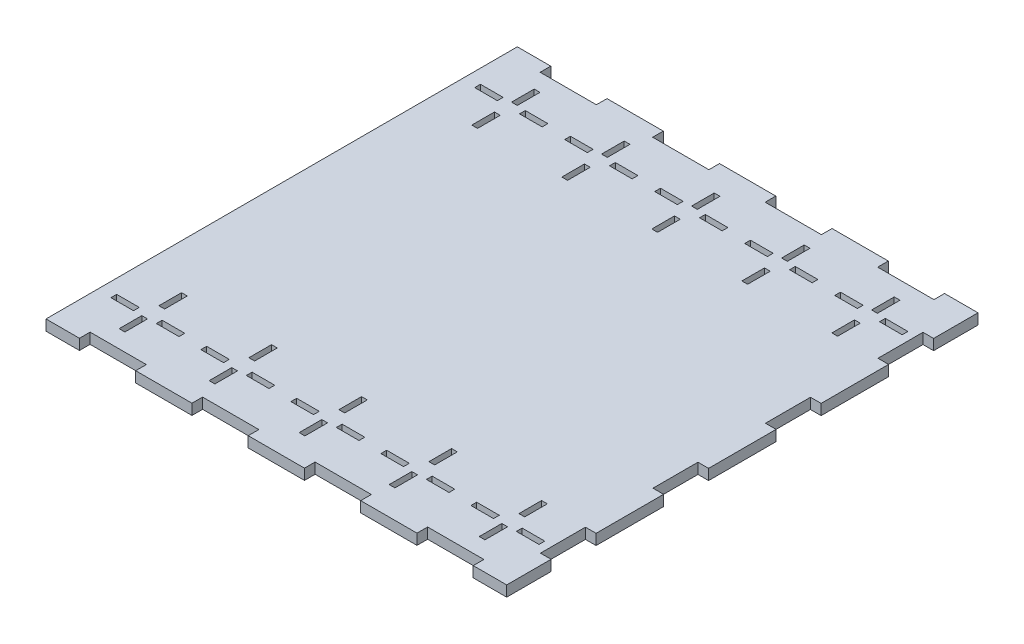
SolidWorks part; units mm, degrees
material "Balsa"
ref_plane "Front Plane" through (0, 0, 0) normal (0, 0, 1) x (1, 0, 0)
ref_plane "Top Plane" through (0, 0, 0) normal (0, 1, 0) x (1, 0, 0)
ref_plane "Right Plane" through (0, 0, 0) normal (1, 0, 0) x (0, 0, -1)
sketch "Sketch1" plane through (0, 0, 0) normal (0, 1, 0) x (1, 0, 0)
  line L0 (0, 133) -> (0, -133) construction
  line L1 (-130, -133) -> (130, -133)
  line L2 (-130, -133) -> (-130, 133)
  line L3 (-130, 133) -> (130, 133)
  line L4 (130, -133) -> (130, 133)
  point P4 (0, 133)
  point P6 (130, 0)
  dimension "D1" = 266
  dimension "D2" = 260
extrude "Boss-Extrude1" add sketch "Sketch1" along normal blind 6 contours L3 L4 L1 L2
sketch "Sketch2" plane through (0, 6, 0) normal (0, 1, 0) x (1, 0, 0)
  line L0 (-130, 0) -> (130, 0) construction
  line L1 (-130, -133) -> (-130, 133) construction
  line L2 (130, -133) -> (130, 133) construction
  line L3 (0, 133) -> (0, -133) construction
  line L4 (-130, 133) -> (130, 133) construction
  line L5 (-130, -133) -> (130, -133) construction
  line L6 (111.125, 133) -> (111.125, 127)
  line L7 (-15.875, 133) -> (-47.625, 133)
  line L8 (-15.875, 133) -> (-15.875, 127)
  line L9 (-15.875, 127) -> (-47.625, 127)
  line L10 (-47.625, 133) -> (-47.625, 127)
  line L11 (-79.375, 133) -> (-111.125, 133)
  line L12 (-79.375, 133) -> (-79.375, 127)
  line L13 (-79.375, 127) -> (-111.125, 127)
  line L14 (-111.125, 133) -> (-111.125, 127)
  line L15 (79.375, 127) -> (111.125, 127)
  line L16 (79.375, 133) -> (79.375, 127)
  line L17 (79.375, 133) -> (111.125, 133)
  line L18 (47.625, 133) -> (47.625, 127)
  line L19 (15.875, 127) -> (47.625, 127)
  line L20 (15.875, 133) -> (15.875, 127)
  line L21 (15.875, 133) -> (47.625, 133)
  line L22 (15.875, -133) -> (47.625, -133)
  line L23 (15.875, -133) -> (15.875, -127)
  line L24 (15.875, -127) -> (47.625, -127)
  line L25 (47.625, -133) -> (47.625, -127)
  line L26 (79.375, -133) -> (111.125, -133)
  line L27 (79.375, -133) -> (79.375, -127)
  line L28 (79.375, -127) -> (111.125, -127)
  line L29 (-111.125, -133) -> (-111.125, -127)
  line L30 (-79.375, -127) -> (-111.125, -127)
  line L31 (-79.375, -133) -> (-79.375, -127)
  line L32 (-79.375, -133) -> (-111.125, -133)
  line L33 (-47.625, -133) -> (-47.625, -127)
  line L34 (-15.875, -127) -> (-47.625, -127)
  line L35 (-15.875, -133) -> (-15.875, -127)
  line L36 (-15.875, -133) -> (-47.625, -133)
  line L37 (111.125, -133) -> (111.125, -127)
  line L38 (130, 133) -> (0, 0) construction
  line L39 (124, -82.55) -> (124, -107.95)
  line L40 (130, 19.05) -> (124, 19.05)
  line L41 (130, 19.05) -> (130, 44.45)
  line L42 (130, 44.45) -> (124, 44.45)
  line L43 (124, 19.05) -> (124, 44.45)
  line L44 (130, 82.55) -> (124, 82.55)
  line L45 (130, 82.55) -> (130, 107.95)
  line L46 (130, 107.95) -> (124, 107.95)
  line L47 (124, 82.55) -> (124, 107.95)
  line L48 (130, -107.95) -> (124, -107.95)
  line L49 (130, -82.55) -> (130, -107.95)
  line L50 (130, -82.55) -> (124, -82.55)
  line L51 (124, -19.05) -> (124, -44.45)
  line L52 (130, -44.45) -> (124, -44.45)
  line L53 (130, -19.05) -> (130, -44.45)
  line L54 (130, -19.05) -> (124, -19.05)
  point P12 (0, 0)
  point P22 (-31.75, 127)
  point P23 (-95.25, 127)
  point P59 (124, 31.75)
  point P60 (130, 31.75)
  point P61 (130, 95.25)
  dimension "D1" = 31.75
  dimension "D2" = 63.5
  dimension "D3" = 63.5
  dimension "D4" = 254
  dimension "D5" = 63.5
  dimension "D6" = 25.4
  dimension "D7" = 63.5
extrude "Tab Cut Outs" cut sketch "Sketch2" against normal up to surface (6 mm away) up to face at (0, 0, 0)
sketch "Sketch3" plane through (0, 6, 0) normal (0, 1, 0) x (1, 0, 0)
  line L104 (79.4766, -127.1016) -> (111.0234, -127.1016)
  line L105 (111.0234, -127.1016) -> (111.0234, -133.1016)
  line L106 (111.0234, -133.1016) -> (130.1016, -133.1016)
  line L107 (130.1016, -133.1016) -> (130.1016, -107.8484)
  line L108 (130.1016, -107.8484) -> (124.1016, -107.8484)
  line L109 (124.1016, -107.8484) -> (124.1016, -82.6516)
  line L110 (124.1016, -82.6516) -> (130.1016, -82.6516)
  line L111 (130.1016, -82.6516) -> (130.1016, -44.3484)
  line L112 (130.1016, -44.3484) -> (124.1016, -44.3484)
  line L113 (124.1016, -44.3484) -> (124.1016, -19.1516)
  line L114 (124.1016, -19.1516) -> (130.1016, -19.1516)
  line L115 (130.1016, -19.1516) -> (130.1016, 19.1516)
  line L116 (130.1016, 19.1516) -> (124.1016, 19.1516)
  line L117 (124.1016, 19.1516) -> (124.1016, 44.3484)
  line L118 (124.1016, 44.3484) -> (130.1016, 44.3484)
  line L119 (130.1016, 44.3484) -> (130.1016, 82.6516)
  line L120 (130.1016, 82.6516) -> (124.1016, 82.6516)
  line L121 (124.1016, 82.6516) -> (124.1016, 107.8484)
  line L122 (124.1016, 107.8484) -> (130.1016, 107.8484)
  line L123 (130.1016, 107.8484) -> (130.1016, 133.1016)
  line L124 (130.1016, 133.1016) -> (111.0234, 133.1016)
  line L125 (111.0234, 133.1016) -> (111.0234, 127.1016)
  line L126 (111.0234, 127.1016) -> (79.4766, 127.1016)
  line L127 (79.4766, 127.1016) -> (79.4766, 133.1016)
  line L128 (79.4766, 133.1016) -> (47.5234, 133.1016)
  line L129 (47.5234, 133.1016) -> (47.5234, 127.1016)
  line L130 (47.5234, 127.1016) -> (15.9766, 127.1016)
  line L131 (15.9766, 127.1016) -> (15.9766, 133.1016)
  line L132 (15.9766, 133.1016) -> (-15.9766, 133.1016)
  line L133 (-15.9766, 133.1016) -> (-15.9766, 127.1016)
  line L134 (-15.9766, 127.1016) -> (-47.5234, 127.1016)
  line L135 (-47.5234, 127.1016) -> (-47.5234, 133.1016)
  line L136 (-47.5234, 133.1016) -> (-79.4766, 133.1016)
  line L137 (-79.4766, 133.1016) -> (-79.4766, 127.1016)
  line L138 (-79.4766, 127.1016) -> (-111.0234, 127.1016)
  line L139 (-111.0234, 127.1016) -> (-111.0234, 133.1016)
  line L140 (-111.0234, 133.1016) -> (-130.1016, 133.1016)
  line L141 (-130.1016, 133.1016) -> (-130.1016, -133.1016)
  line L142 (-130.1016, -133.1016) -> (-111.0234, -133.1016)
  line L143 (-111.0234, -133.1016) -> (-111.0234, -127.1016)
  line L144 (-111.0234, -127.1016) -> (-79.4766, -127.1016)
  line L145 (-79.4766, -127.1016) -> (-79.4766, -133.1016)
  line L146 (-79.4766, -133.1016) -> (-47.5234, -133.1016)
  line L147 (-47.5234, -133.1016) -> (-47.5234, -127.1016)
  line L148 (-47.5234, -127.1016) -> (-15.9766, -127.1016)
  line L149 (-15.9766, -127.1016) -> (-15.9766, -133.1016)
  line L150 (-15.9766, -133.1016) -> (15.9766, -133.1016)
  line L151 (15.9766, -133.1016) -> (15.9766, -127.1016)
  line L152 (15.9766, -127.1016) -> (47.5234, -127.1016)
  line L153 (47.5234, -127.1016) -> (47.5234, -133.1016)
  line L154 (47.5234, -133.1016) -> (79.4766, -133.1016)
  line L155 (79.4766, -133.1016) -> (79.4766, -127.1016)
  line L156 (79.4766, -127.1016) -> (111.0234, -127.1016)
  line L157 (111.0234, -127.1016) -> (111.0234, -133.1016)
  line L158 (111.0234, -133.1016) -> (130.1016, -133.1016)
  line L159 (130.1016, -133.1016) -> (130.1016, -107.8484)
  line L160 (130.1016, -107.8484) -> (124.1016, -107.8484)
  line L161 (124.1016, -107.8484) -> (124.1016, -82.6516)
  line L162 (124.1016, -82.6516) -> (130.1016, -82.6516)
  line L163 (130.1016, -82.6516) -> (130.1016, -44.3484)
  line L164 (130.1016, -44.3484) -> (124.1016, -44.3484)
  line L165 (124.1016, -44.3484) -> (124.1016, -19.1516)
  line L166 (124.1016, -19.1516) -> (130.1016, -19.1516)
  line L167 (130.1016, -19.1516) -> (130.1016, 19.1516)
  line L168 (130.1016, 19.1516) -> (124.1016, 19.1516)
  line L169 (124.1016, 19.1516) -> (124.1016, 44.3484)
  line L170 (124.1016, 44.3484) -> (130.1016, 44.3484)
  line L171 (130.1016, 44.3484) -> (130.1016, 82.6516)
  line L172 (130.1016, 82.6516) -> (124.1016, 82.6516)
  line L173 (124.1016, 82.6516) -> (124.1016, 107.8484)
  line L174 (124.1016, 107.8484) -> (130.1016, 107.8484)
  line L175 (130.1016, 107.8484) -> (130.1016, 133.1016)
  line L176 (130.1016, 133.1016) -> (111.0234, 133.1016)
  line L177 (111.0234, 133.1016) -> (111.0234, 127.1016)
  line L178 (111.0234, 127.1016) -> (79.4766, 127.1016)
  line L179 (79.4766, 127.1016) -> (79.4766, 133.1016)
  line L180 (79.4766, 133.1016) -> (47.5234, 133.1016)
  line L181 (47.5234, 133.1016) -> (47.5234, 127.1016)
  line L182 (47.5234, 127.1016) -> (15.9766, 127.1016)
  line L183 (15.9766, 127.1016) -> (15.9766, 133.1016)
  line L184 (15.9766, 133.1016) -> (-15.9766, 133.1016)
  line L185 (-15.9766, 133.1016) -> (-15.9766, 127.1016)
  line L186 (-15.9766, 127.1016) -> (-47.5234, 127.1016)
  line L187 (-47.5234, 127.1016) -> (-47.5234, 133.1016)
  line L188 (-47.5234, 133.1016) -> (-79.4766, 133.1016)
  line L189 (-79.4766, 133.1016) -> (-79.4766, 127.1016)
  line L190 (-79.4766, 127.1016) -> (-111.0234, 127.1016)
  line L191 (-111.0234, 127.1016) -> (-111.0234, 133.1016)
  line L192 (-111.0234, 133.1016) -> (-130.1016, 133.1016)
  line L193 (-130.1016, 133.1016) -> (-130.1016, -133.1016)
  line L194 (-130.1016, -133.1016) -> (-111.0234, -133.1016)
  line L195 (-111.0234, -133.1016) -> (-111.0234, -127.1016)
  line L196 (-111.0234, -127.1016) -> (-79.4766, -127.1016)
  line L197 (-79.4766, -127.1016) -> (-79.4766, -133.1016)
  line L198 (-79.4766, -133.1016) -> (-47.5234, -133.1016)
  line L199 (-47.5234, -133.1016) -> (-47.5234, -127.1016)
  line L200 (-47.5234, -127.1016) -> (-15.9766, -127.1016)
  line L201 (-15.9766, -127.1016) -> (-15.9766, -133.1016)
  line L202 (-15.9766, -133.1016) -> (15.9766, -133.1016)
  line L203 (15.9766, -133.1016) -> (15.9766, -127.1016)
  line L204 (15.9766, -127.1016) -> (47.5234, -127.1016)
  line L205 (47.5234, -127.1016) -> (47.5234, -133.1016)
  line L206 (47.5234, -133.1016) -> (79.4766, -133.1016)
  line L207 (79.4766, -133.1016) -> (79.4766, -127.1016)
  dimension "D1" = 0.1016
extrude "KERF" [suppressed] add sketch "Sketch3" against normal up to surface (6 mm away)
sketch "Sketch4" plane through (0, 6, 0) normal (0, 1, 0) x (1, 0, 0)
  line L0 (-130, -133) -> (-130, 133) construction
  line L5 (-58.5244, 101.0412) -> (-71.3006, 101.0412)
  line L6 (-58.5244, 104.2924) -> (-71.3006, 104.2924)
  line L7 (-130, 0) -> (130, 0) construction
  line L8 (-104.6, 81.915) -> (-101.3488, 81.915)
  line L9 (-104.6, 81.915) -> (-104.6, 94.6912)
  line L10 (-104.6, 94.6912) -> (-101.3488, 94.6912)
  line L11 (-101.3488, 81.915) -> (-101.3488, 94.6912)
  line L12 (-104.6, 104.3432) -> (-101.3488, 104.3432)
  line L13 (-104.6, 104.3432) -> (-104.6, 117.1194)
  line L14 (-104.6, 117.1194) -> (-101.3488, 117.1194)
  line L15 (-101.3488, 104.3432) -> (-101.3488, 117.1194)
  line L113 (-71.3006, 101.0412) -> (-71.3006, 104.2924)
  line L114 (-58.5244, 101.0412) -> (-58.5244, 104.2924)
  line L115 (-53.8, 104.3432) -> (-53.8, 117.1194)
  line L135 (130, -19.05) -> (130, 19.05) construction
  line L136 (-102.9744, 104.3432) -> (-102.9744, 92.7646) construction
  line L137 (-53.8, 104.3432) -> (-50.5488, 104.3432)
  line L138 (-109.3244, 101.0412) -> (-122.1006, 101.0412)
  line L139 (-109.3244, 101.0412) -> (-109.3244, 104.2924)
  line L140 (-109.3244, 104.2924) -> (-122.1006, 104.2924)
  line L141 (-122.1006, 101.0412) -> (-122.1006, 104.2924)
  line L142 (-96.6244, 100.8544) -> (-83.8482, 100.8544)
  line L143 (-96.6244, 100.8544) -> (-96.6244, 104.1056)
  line L144 (-96.6244, 104.1056) -> (-83.8482, 104.1056)
  line L145 (-83.8482, 100.8544) -> (-83.8482, 104.1056)
  line L146 (-50.5488, 104.3432) -> (-50.5488, 117.1194)
  line L147 (-53.8, 117.1194) -> (-50.5488, 117.1194)
  line L148 (-45.8244, 100.8544) -> (-45.8244, 104.1056)
  line L149 (-45.8244, 100.8544) -> (-33.0482, 100.8544)
  line L150 (-33.0482, 100.8544) -> (-33.0482, 104.1056)
  line L151 (-45.8244, 104.1056) -> (-33.0482, 104.1056)
  line L152 (-53.8, 81.915) -> (-53.8, 94.6912)
  line L153 (-53.8, 81.915) -> (-50.5488, 81.915)
  line L154 (-50.5488, 81.915) -> (-50.5488, 94.6912)
  line L155 (-53.8, 94.6912) -> (-50.5488, 94.6912)
  line L156 (-7.7244, 101.0412) -> (-20.5006, 101.0412)
  line L157 (-7.7244, 104.2924) -> (-20.5006, 104.2924)
  line L158 (-20.5006, 101.0412) -> (-20.5006, 104.2924)
  line L159 (-7.7244, 101.0412) -> (-7.7244, 104.2924)
  line L160 (-3, 104.3432) -> (-3, 117.1194)
  line L161 (-3, 104.3432) -> (0.2512, 104.3432)
  line L162 (0.2512, 104.3432) -> (0.2512, 117.1194)
  line L163 (-3, 117.1194) -> (0.2512, 117.1194)
  line L164 (4.9756, 100.8544) -> (4.9756, 104.1056)
  line L165 (4.9756, 100.8544) -> (17.7518, 100.8544)
  line L166 (17.7518, 100.8544) -> (17.7518, 104.1056)
  line L167 (4.9756, 104.1056) -> (17.7518, 104.1056)
  line L168 (-3, 81.915) -> (-3, 94.6912)
  line L169 (-3, 81.915) -> (0.2512, 81.915)
  line L170 (0.2512, 81.915) -> (0.2512, 94.6912)
  line L171 (-3, 94.6912) -> (0.2512, 94.6912)
  line L172 (43.0756, 101.0412) -> (30.2994, 101.0412)
  line L173 (43.0756, 104.2924) -> (30.2994, 104.2924)
  line L174 (30.2994, 101.0412) -> (30.2994, 104.2924)
  line L175 (43.0756, 101.0412) -> (43.0756, 104.2924)
  line L176 (47.8, 104.3432) -> (47.8, 117.1194)
  line L177 (47.8, 104.3432) -> (51.0512, 104.3432)
  line L178 (51.0512, 104.3432) -> (51.0512, 117.1194)
  line L179 (47.8, 117.1194) -> (51.0512, 117.1194)
  line L180 (55.7756, 100.8544) -> (55.7756, 104.1056)
  line L181 (55.7756, 100.8544) -> (68.5518, 100.8544)
  line L182 (68.5518, 100.8544) -> (68.5518, 104.1056)
  line L183 (55.7756, 104.1056) -> (68.5518, 104.1056)
  line L184 (47.8, 81.915) -> (47.8, 94.6912)
  line L185 (47.8, 81.915) -> (51.0512, 81.915)
  line L186 (51.0512, 81.915) -> (51.0512, 94.6912)
  line L187 (47.8, 94.6912) -> (51.0512, 94.6912)
  line L188 (93.8756, 101.0412) -> (81.0994, 101.0412)
  line L189 (93.8756, 104.2924) -> (81.0994, 104.2924)
  line L190 (81.0994, 101.0412) -> (81.0994, 104.2924)
  line L191 (93.8756, 101.0412) -> (93.8756, 104.2924)
  line L192 (98.6, 104.3432) -> (98.6, 117.1194)
  line L193 (98.6, 104.3432) -> (101.8512, 104.3432)
  line L194 (101.8512, 104.3432) -> (101.8512, 117.1194)
  line L195 (98.6, 117.1194) -> (101.8512, 117.1194)
  line L196 (106.5756, 100.8544) -> (106.5756, 104.1056)
  line L197 (106.5756, 100.8544) -> (119.3518, 100.8544)
  line L198 (119.3518, 100.8544) -> (119.3518, 104.1056)
  line L199 (106.5756, 104.1056) -> (119.3518, 104.1056)
  line L200 (98.6, 81.915) -> (98.6, 94.6912)
  line L201 (98.6, 81.915) -> (101.8512, 81.915)
  line L202 (101.8512, 81.915) -> (101.8512, 94.6912)
  line L203 (98.6, 94.6912) -> (101.8512, 94.6912)
  line L204 (-102.9744, -104.3432) -> (-102.9744, -92.7646) construction
  line L205 (-53.8, -94.6912) -> (-50.5488, -94.6912)
  line L206 (-50.5488, -81.915) -> (-50.5488, -94.6912)
  line L207 (-53.8, -81.915) -> (-50.5488, -81.915)
  line L208 (-53.8, -81.915) -> (-53.8, -94.6912)
  line L209 (-45.8244, -104.1056) -> (-33.0482, -104.1056)
  line L210 (-33.0482, -100.8544) -> (-33.0482, -104.1056)
  line L211 (-45.8244, -100.8544) -> (-33.0482, -100.8544)
  line L212 (-45.8244, -100.8544) -> (-45.8244, -104.1056)
  line L213 (-53.8, -117.1194) -> (-50.5488, -117.1194)
  line L214 (-50.5488, -104.3432) -> (-50.5488, -117.1194)
  line L215 (-53.8, -104.3432) -> (-50.5488, -104.3432)
  line L216 (-53.8, -104.3432) -> (-53.8, -117.1194)
  line L217 (-58.5244, -101.0412) -> (-58.5244, -104.2924)
  line L218 (-71.3006, -101.0412) -> (-71.3006, -104.2924)
  line L219 (-58.5244, -104.2924) -> (-71.3006, -104.2924)
  line L220 (-58.5244, -101.0412) -> (-71.3006, -101.0412)
  line L221 (-3, -94.6912) -> (0.2512, -94.6912)
  line L222 (0.2512, -81.915) -> (0.2512, -94.6912)
  line L223 (-3, -81.915) -> (0.2512, -81.915)
  line L224 (-3, -81.915) -> (-3, -94.6912)
  line L225 (4.9756, -104.1056) -> (17.7518, -104.1056)
  line L226 (17.7518, -100.8544) -> (17.7518, -104.1056)
  line L227 (4.9756, -100.8544) -> (17.7518, -100.8544)
  line L228 (4.9756, -100.8544) -> (4.9756, -104.1056)
  line L229 (-3, -117.1194) -> (0.2512, -117.1194)
  line L230 (0.2512, -104.3432) -> (0.2512, -117.1194)
  line L231 (-3, -104.3432) -> (0.2512, -104.3432)
  line L232 (-3, -104.3432) -> (-3, -117.1194)
  line L233 (-7.7244, -101.0412) -> (-7.7244, -104.2924)
  line L234 (-20.5006, -101.0412) -> (-20.5006, -104.2924)
  line L235 (-7.7244, -104.2924) -> (-20.5006, -104.2924)
  line L236 (-7.7244, -101.0412) -> (-20.5006, -101.0412)
  line L237 (47.8, -94.6912) -> (51.0512, -94.6912)
  line L238 (51.0512, -81.915) -> (51.0512, -94.6912)
  line L239 (47.8, -81.915) -> (51.0512, -81.915)
  line L240 (47.8, -81.915) -> (47.8, -94.6912)
  line L241 (55.7756, -100.8544) -> (55.7756, -104.1056)
  line L242 (47.8, -117.1194) -> (51.0512, -117.1194)
  line L243 (51.0512, -104.3432) -> (51.0512, -117.1194)
  line L244 (47.8, -104.3432) -> (51.0512, -104.3432)
  line L245 (47.8, -104.3432) -> (47.8, -117.1194)
  line L246 (43.0756, -101.0412) -> (43.0756, -104.2924)
  line L247 (30.2994, -101.0412) -> (30.2994, -104.2924)
  line L248 (43.0756, -104.2924) -> (30.2994, -104.2924)
  line L249 (43.0756, -101.0412) -> (30.2994, -101.0412)
  line L250 (119.3518, -100.8544) -> (119.3518, -104.1056)
  line L251 (98.6, -94.6912) -> (101.8512, -94.6912)
  line L252 (101.8512, -81.915) -> (101.8512, -94.6912)
  line L253 (98.6, -81.915) -> (101.8512, -81.915)
  line L254 (98.6, -81.915) -> (98.6, -94.6912)
  line L255 (106.5756, -104.1056) -> (119.3518, -104.1056)
  line L256 (106.5756, -100.8544) -> (119.3518, -100.8544)
  line L257 (106.5756, -100.8544) -> (106.5756, -104.1056)
  line L258 (98.6, -104.3432) -> (101.8512, -104.3432)
  line L259 (93.8756, -101.0412) -> (93.8756, -104.2924)
  line L260 (81.0994, -101.0412) -> (81.0994, -104.2924)
  line L261 (93.8756, -104.2924) -> (81.0994, -104.2924)
  line L262 (93.8756, -101.0412) -> (81.0994, -101.0412)
  line L263 (55.7756, -104.1056) -> (68.5518, -104.1056)
  line L264 (68.5518, -100.8544) -> (68.5518, -104.1056)
  line L265 (55.7756, -100.8544) -> (68.5518, -100.8544)
  line L266 (98.6, -117.1194) -> (101.8512, -117.1194)
  line L267 (101.8512, -104.3432) -> (101.8512, -117.1194)
  line L268 (98.6, -104.3432) -> (98.6, -117.1194)
  line L269 (-104.6, -94.6912) -> (-101.3488, -94.6912)
  line L270 (-101.3488, -81.915) -> (-101.3488, -94.6912)
  line L271 (-104.6, -81.915) -> (-101.3488, -81.915)
  line L272 (-104.6, -81.915) -> (-104.6, -94.6912)
  line L273 (-96.6244, -104.1056) -> (-83.8482, -104.1056)
  line L274 (-83.8482, -100.8544) -> (-83.8482, -104.1056)
  line L275 (-96.6244, -100.8544) -> (-83.8482, -100.8544)
  line L276 (-96.6244, -100.8544) -> (-96.6244, -104.1056)
  line L277 (-104.6, -117.1194) -> (-101.3488, -117.1194)
  line L278 (-101.3488, -104.3432) -> (-101.3488, -117.1194)
  line L279 (-104.6, -104.3432) -> (-101.3488, -104.3432)
  line L280 (-104.6, -104.3432) -> (-104.6, -117.1194)
  line L281 (-109.3244, -101.0412) -> (-109.3244, -104.2924)
  line L282 (-122.1006, -101.0412) -> (-122.1006, -104.2924)
  line L283 (-109.3244, -104.2924) -> (-122.1006, -104.2924)
  line L284 (-109.3244, -101.0412) -> (-122.1006, -101.0412)
  dimension "D2" = 81.915
  dimension "D3" = 3.2512
  dimension "D4" = 3.2512
  dimension "D5" = 12.7762
  dimension "D6" = 25.4
  dimension "D7" = 25.4
  dimension "D8" = 3.2512
  dimension "D9" = 12.7762
  dimension "D10" = 3.2512
  dimension "D11" = 5
  dimension "D12" = 12.7762
  dimension "D13" = 12.7762
  dimension "D14" = 6.35
  dimension "D15" = 12.7
  dimension "D16" = 6.35
  dimension "D17" = 9.652
extrude "Cut-Extrude1" cut sketch "Sketch4" against normal through all
